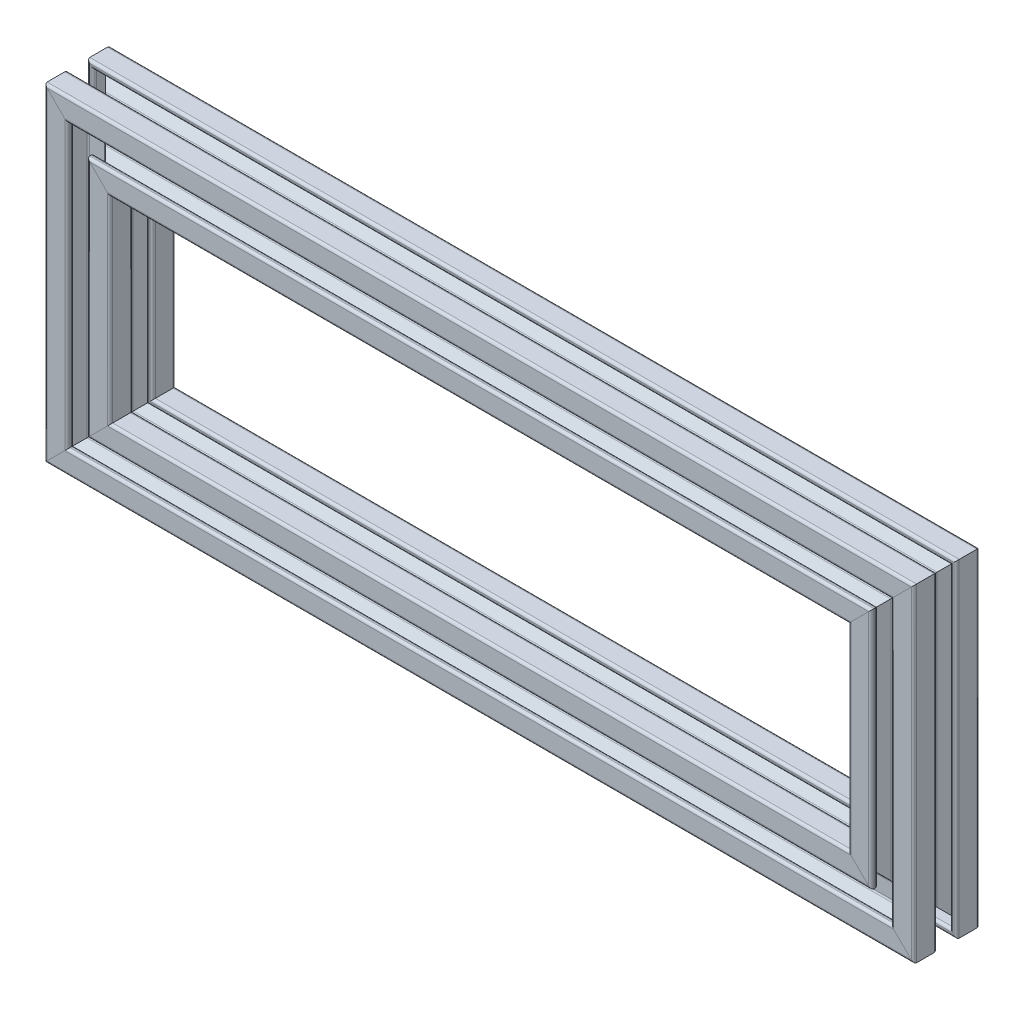
SolidWorks part; units mm, degrees
material "1060 Alloy"
material "1060 Alloy"
material "1060 Alloy"
ref_plane "Front Plane" through (0, 0, 0) normal (0, 0, 1) x (1, 0, 0)
ref_plane "Top Plane" through (0, 0, 0) normal (0, 1, 0) x (1, 0, 0)
ref_plane "Right Plane" through (0, 0, 0) normal (1, 0, 0) x (0, 0, -1)
sketch "Sketch2" plane through (0, 0, 0) normal (0, 0, 1) x (1, 0, 0)
  line L1 (-122.5, -40) -> (122.5, -40)
  line L2 (-122.5, -40) -> (-122.5, 40)
  line L3 (-122.5, 40) -> (122.5, 40)
  line L4 (122.5, -40) -> (122.5, 40)
  line L5 (-122.5, -40) -> (122.5, 40) construction
  line L6 (-122.5, 40) -> (122.5, -40) construction
  point P0 (0, 0)
  dimension "D1" = 245
  dimension "D2" = 80
other "Profile 4X4(1)"
ref_plane "Plane3" through (-122.5, 40, 0) normal (1, 0, 0) x (0, 1, 0)
sketch "Sketch1" plane through (-122.5, 40, 0) normal (1, 0, 0) x (0, 1, 0)
  line L0 (-3, 9.2) -> (-3, 8.8)
  line L1 (-2.2544, 4) -> (2.2544, 4)
  line L2 (-4, 2.2544) -> (-4, -2.2544)
  line L3 (-2.2544, -4) -> (2.2544, -4)
  line L4 (4, 2.2544) -> (4, -2.2544)
  line L7 (-6.5858, 8) -> (-3.8, 8)
  line L8 (-8, 6.5858) -> (-8, 3.8)
  line L9 (-6.5858, -8) -> (-3.8, -8)
  line L10 (8, 6.5858) -> (8, 3.8)
  line L12 (9.7657, -9.7657) -> (10, -10) construction
  line L13 (-9.2, 10) -> (-3.8, 10)
  line L14 (-10, 9.2) -> (-10, 3.8)
  line L15 (-9.2, -10) -> (-3.8, -10)
  line L16 (10, 9.2) -> (10, 3.8)
  line L17 (-10, 10) -> (-9.7657, 9.7657) construction
  line L18 (-10, -10) -> (-9.7657, -9.7657) construction
  line L21 (3, 9.2) -> (3, 8.8)
  line L22 (3, -9.2) -> (3, -8.8)
  line L23 (-3, -9.2) -> (-3, -8.8)
  line L24 (3.8, 10) -> (9.2, 10)
  line L25 (3.8, 8) -> (6.5858, 8)
  line L26 (-9.2, 3) -> (-8.8, 3)
  line L27 (9.2, 3) -> (8.8, 3)
  line L28 (9.2, -3) -> (8.8, -3)
  line L29 (-9.2, -3) -> (-8.8, -3)
  line L30 (-10, -3.8) -> (-10, -9.2)
  line L31 (-8, -3.8) -> (-8, -6.5858)
  line L32 (8, -3.8) -> (8, -6.5858)
  line L33 (10, -3.8) -> (10, -9.2)
  line L34 (3.8, -8) -> (6.5858, -8)
  line L35 (3.8, -10) -> (9.2, -10)
  line L36 (6.5858, 8) -> (2.8201, 4.2343)
  line L37 (8, 6.5858) -> (4.2343, 2.8201)
  line L38 (8, -6.5858) -> (4.2343, -2.8201)
  line L39 (6.5858, -8) -> (2.8201, -4.2343)
  line L40 (-6.5858, -8) -> (-2.8201, -4.2343)
  line L41 (-8, -6.5858) -> (-4.2343, -2.8201)
  line L42 (-8, 6.5858) -> (-4.2343, 2.8201)
  line L43 (-6.5858, 8) -> (-2.8201, 4.2343)
  line L47 (9.7657, 9.7657) -> (10, 10) construction
  circle A0 centre (0, 0) radius 2
  arc A1 (9.2, -3) -> (10, -3.8) centre (9.2, -3.8) cw
  arc A2 (8.8, -3) -> (8, -3.8) centre (8.8, -3.8) ccw
  arc A3 (3, -9.2) -> (3.8, -10) centre (3.8, -9.2) ccw
  arc A4 (3, -8.8) -> (3.8, -8) centre (3.8, -8.8) cw
  arc A5 (-3, -9.2) -> (-3.8, -10) centre (-3.8, -9.2) cw
  arc A6 (-3, -8.8) -> (-3.8, -8) centre (-3.8, -8.8) ccw
  arc A7 (-8.8, -3) -> (-8, -3.8) centre (-8.8, -3.8) cw
  arc A8 (-9.2, -3) -> (-10, -3.8) centre (-9.2, -3.8) ccw
  arc A9 (-10, -9.2) -> (-9.2, -10) centre (-9.2, -9.2) ccw
  arc A10 (9.2, -10) -> (10, -9.2) centre (9.2, -9.2) ccw
  arc A11 (9.2, 10) -> (10, 9.2) centre (9.2, 9.2) cw
  arc A12 (-9.2, 10) -> (-10, 9.2) centre (-9.2, 9.2) ccw
  arc A13 (9.2, 3) -> (10, 3.8) centre (9.2, 3.8) ccw
  arc A14 (8.8, 3) -> (8, 3.8) centre (8.8, 3.8) cw
  arc A15 (3, 9.2) -> (3.8, 10) centre (3.8, 9.2) cw
  arc A16 (3, 8.8) -> (3.8, 8) centre (3.8, 8.8) ccw
  arc A17 (-3, 9.2) -> (-3.8, 10) centre (-3.8, 9.2) ccw
  arc A18 (-3, 8.8) -> (-3.8, 8) centre (-3.8, 8.8) cw
  arc A19 (-8.8, 3) -> (-8, 3.8) centre (-8.8, 3.8) ccw
  arc A20 (-9.2, 3) -> (-10, 3.8) centre (-9.2, 3.8) cw
  arc A21 (-2.8201, 4.2343) -> (-2.2544, 4) centre (-2.2544, 4.8) ccw
  arc A22 (4.2343, 2.8201) -> (4, 2.2544) centre (4.8, 2.2544) ccw
  arc A23 (2.8201, 4.2343) -> (2.2544, 4) centre (2.2544, 4.8) cw
  arc A24 (4.2343, -2.8201) -> (4, -2.2544) centre (4.8, -2.2544) cw
  arc A25 (2.8201, -4.2343) -> (2.2544, -4) centre (2.2544, -4.8) ccw
  arc A26 (-2.8201, -4.2343) -> (-2.2544, -4) centre (-2.2544, -4.8) cw
  arc A27 (-4.2343, -2.8201) -> (-4, -2.2544) centre (-4.8, -2.2544) ccw
  arc A28 (-4.2343, 2.8201) -> (-4, 2.2544) centre (-4.8, 2.2544) cw
  point P7 (0, 0)
  point P10 (-2.5858, 4)
  point P53 (10, -3)
  point P56 (8, -3)
  point P59 (3, -10)
  point P62 (3, -8)
  point P65 (-3, -10)
  point P68 (-3, -8)
  point P71 (-8, -3)
  point P74 (-10, -3)
  point P89 (10, 3)
  point P92 (8, 3)
  point P95 (3, 10)
  point P98 (3, 8)
  point P101 (-3, 10)
  point P104 (-3, 8)
  point P107 (-8, 3)
  point P110 (-10, 3)
  point P116 (4, 2.5858)
  point P119 (2.5858, 4)
  point P122 (4, -2.5858)
  point P125 (2.5858, -4)
  point P128 (-2.5858, -4)
  point P131 (-4, -2.5858)
  point P134 (-4, 2.5858)
  dimension "D3" = 4
  dimension "D11" = 0.8
  dimension "D12" = 0.8
  dimension "D2" = 0.8
  dimension "D4" = 20
  dimension "D6" = 20
  dimension "D8" = 7
  dimension "D9" = 7
other "Profile 4X4(2)"
ref_plane "Plane4" through (-122.5, -40, 0) normal (0, 1, 0) x (-1, 0, 0)
sketch "Sketch11" plane through (-122.5, -40, 0) normal (0, 1, 0) x (-1, 0, 0)
  line L0 (-3, 9.2) -> (-3, 8.8)
  line L1 (-2.2544, 4) -> (2.2544, 4)
  line L2 (-4, 2.2544) -> (-4, -2.2544)
  line L3 (-2.2544, -4) -> (2.2544, -4)
  line L4 (4, 2.2544) -> (4, -2.2544)
  line L7 (-6.5858, 8) -> (-3.8, 8)
  line L8 (-8, 6.5858) -> (-8, 3.8)
  line L9 (-6.5858, -8) -> (-3.8, -8)
  line L10 (8, 6.5858) -> (8, 3.8)
  line L12 (9.7657, -9.7657) -> (10, -10) construction
  line L13 (-9.2, 10) -> (-3.8, 10)
  line L14 (-10, 9.2) -> (-10, 3.8)
  line L15 (-9.2, -10) -> (-3.8, -10)
  line L16 (10, 9.2) -> (10, 3.8)
  line L17 (-10, 10) -> (-9.7657, 9.7657) construction
  line L18 (-10, -10) -> (-9.7657, -9.7657) construction
  line L21 (3, 9.2) -> (3, 8.8)
  line L22 (3, -9.2) -> (3, -8.8)
  line L23 (-3, -9.2) -> (-3, -8.8)
  line L24 (3.8, 10) -> (9.2, 10)
  line L25 (3.8, 8) -> (6.5858, 8)
  line L26 (-9.2, 3) -> (-8.8, 3)
  line L27 (9.2, 3) -> (8.8, 3)
  line L28 (9.2, -3) -> (8.8, -3)
  line L29 (-9.2, -3) -> (-8.8, -3)
  line L30 (-10, -3.8) -> (-10, -9.2)
  line L31 (-8, -3.8) -> (-8, -6.5858)
  line L32 (8, -3.8) -> (8, -6.5858)
  line L33 (10, -3.8) -> (10, -9.2)
  line L34 (3.8, -8) -> (6.5858, -8)
  line L35 (3.8, -10) -> (9.2, -10)
  line L36 (6.5858, 8) -> (2.8201, 4.2343)
  line L37 (8, 6.5858) -> (4.2343, 2.8201)
  line L38 (8, -6.5858) -> (4.2343, -2.8201)
  line L39 (6.5858, -8) -> (2.8201, -4.2343)
  line L40 (-6.5858, -8) -> (-2.8201, -4.2343)
  line L41 (-8, -6.5858) -> (-4.2343, -2.8201)
  line L42 (-8, 6.5858) -> (-4.2343, 2.8201)
  line L43 (-6.5858, 8) -> (-2.8201, 4.2343)
  line L47 (9.7657, 9.7657) -> (10, 10) construction
  circle A0 centre (0, 0) radius 2
  arc A1 (9.2, -3) -> (10, -3.8) centre (9.2, -3.8) cw
  arc A2 (8.8, -3) -> (8, -3.8) centre (8.8, -3.8) ccw
  arc A3 (3, -9.2) -> (3.8, -10) centre (3.8, -9.2) ccw
  arc A4 (3, -8.8) -> (3.8, -8) centre (3.8, -8.8) cw
  arc A5 (-3, -9.2) -> (-3.8, -10) centre (-3.8, -9.2) cw
  arc A6 (-3, -8.8) -> (-3.8, -8) centre (-3.8, -8.8) ccw
  arc A7 (-8.8, -3) -> (-8, -3.8) centre (-8.8, -3.8) cw
  arc A8 (-9.2, -3) -> (-10, -3.8) centre (-9.2, -3.8) ccw
  arc A9 (-10, -9.2) -> (-9.2, -10) centre (-9.2, -9.2) ccw
  arc A10 (9.2, -10) -> (10, -9.2) centre (9.2, -9.2) ccw
  arc A11 (9.2, 10) -> (10, 9.2) centre (9.2, 9.2) cw
  arc A12 (-9.2, 10) -> (-10, 9.2) centre (-9.2, 9.2) ccw
  arc A13 (9.2, 3) -> (10, 3.8) centre (9.2, 3.8) ccw
  arc A14 (8.8, 3) -> (8, 3.8) centre (8.8, 3.8) cw
  arc A15 (3, 9.2) -> (3.8, 10) centre (3.8, 9.2) cw
  arc A16 (3, 8.8) -> (3.8, 8) centre (3.8, 8.8) ccw
  arc A17 (-3, 9.2) -> (-3.8, 10) centre (-3.8, 9.2) ccw
  arc A18 (-3, 8.8) -> (-3.8, 8) centre (-3.8, 8.8) cw
  arc A19 (-8.8, 3) -> (-8, 3.8) centre (-8.8, 3.8) ccw
  arc A20 (-9.2, 3) -> (-10, 3.8) centre (-9.2, 3.8) cw
  arc A21 (-2.8201, 4.2343) -> (-2.2544, 4) centre (-2.2544, 4.8) ccw
  arc A22 (4.2343, 2.8201) -> (4, 2.2544) centre (4.8, 2.2544) ccw
  arc A23 (2.8201, 4.2343) -> (2.2544, 4) centre (2.2544, 4.8) cw
  arc A24 (4.2343, -2.8201) -> (4, -2.2544) centre (4.8, -2.2544) cw
  arc A25 (2.8201, -4.2343) -> (2.2544, -4) centre (2.2544, -4.8) ccw
  arc A26 (-2.8201, -4.2343) -> (-2.2544, -4) centre (-2.2544, -4.8) cw
  arc A27 (-4.2343, -2.8201) -> (-4, -2.2544) centre (-4.8, -2.2544) ccw
  arc A28 (-4.2343, 2.8201) -> (-4, 2.2544) centre (-4.8, 2.2544) cw
  point P7 (0, 0)
  point P10 (-2.5858, 4)
  point P53 (10, -3)
  point P56 (8, -3)
  point P59 (3, -10)
  point P62 (3, -8)
  point P65 (-3, -10)
  point P68 (-3, -8)
  point P71 (-8, -3)
  point P74 (-10, -3)
  point P89 (10, 3)
  point P92 (8, 3)
  point P95 (3, 10)
  point P98 (3, 8)
  point P101 (-3, 10)
  point P104 (-3, 8)
  point P107 (-8, 3)
  point P110 (-10, 3)
  point P116 (4, 2.5858)
  point P119 (2.5858, 4)
  point P122 (4, -2.5858)
  point P125 (2.5858, -4)
  point P128 (-2.5858, -4)
  point P131 (-4, -2.5858)
  point P134 (-4, 2.5858)
  dimension "D3" = 4
  dimension "D11" = 0.8
  dimension "D12" = 0.8
  dimension "D2" = 0.8
  dimension "D4" = 20
  dimension "D6" = 20
  dimension "D8" = 7
  dimension "D9" = 7
other "Trim/Extend1"
other "Trim/Extend2"
other "Trim/Extend3"
other "Trim/Extend4"
